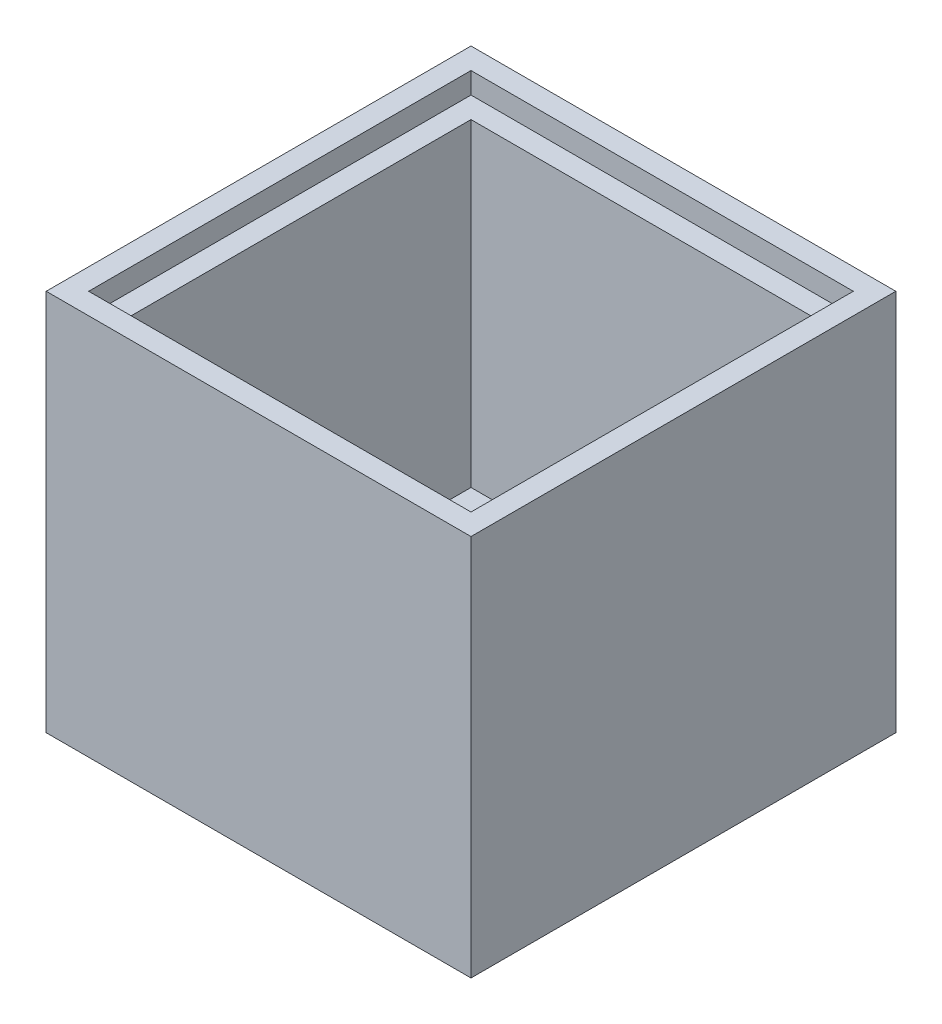
SolidWorks part; units mm, degrees
ref_plane "Alzado" through (0, 0, 0) normal (0, 0, 1) x (1, 0, 0)
ref_plane "Planta" through (0, 0, 0) normal (0, 1, 0) x (1, 0, 0)
ref_plane "Vista lateral" through (0, 0, 0) normal (1, 0, 0) x (0, 0, -1)
sketch "Croquis1" plane through (0, 0, 0) normal (0, 1, 0) x (1, 0, 0)
  line L1 (25, -25) -> (-25, -25)
  line L2 (25, -25) -> (25, 25)
  line L3 (25, 25) -> (-25, 25)
  line L4 (-25, -25) -> (-25, 25)
  line L5 (25, -25) -> (-25, 25) construction
  line L6 (25, 25) -> (-25, -25) construction
  point P0 (0, 0)
  dimension "D1" = 50
  dimension "D2" = 50
extrude "Saliente-Extruir1" add sketch "Croquis1" along normal blind 45
sketch "Croquis2" plane through (0, 45, 0) normal (0, 1, 0) x (1, 0, 0)
  line L1 (20, -20) -> (-20, -20)
  line L2 (20, -20) -> (20, 20)
  line L3 (20, 20) -> (-20, 20)
  line L4 (-20, -20) -> (-20, 20)
  line L5 (20, -20) -> (-20, 20) construction
  line L6 (20, 20) -> (-20, -20) construction
  point P0 (0, 0)
  dimension "D1" = 40
  dimension "D2" = 40
extrude "Cortar-Extruir1" cut sketch "Croquis2" against normal blind 40
sketch "Croquis3" plane through (0, 45, 0) normal (0, 1, 0) x (1, 0, 0)
  line L1 (22.5, -22.5) -> (-22.5, -22.5)
  line L2 (22.5, -22.5) -> (22.5, 22.5)
  line L3 (22.5, 22.5) -> (-22.5, 22.5)
  line L4 (-22.5, -22.5) -> (-22.5, 22.5)
  line L5 (22.5, -22.5) -> (-22.5, 22.5) construction
  line L6 (22.5, 22.5) -> (-22.5, -22.5) construction
  point P0 (0, 0)
  dimension "D1" = 45
  dimension "D2" = 45
extrude "Cortar-Extruir2" cut sketch "Croquis3" against normal blind 2.5
